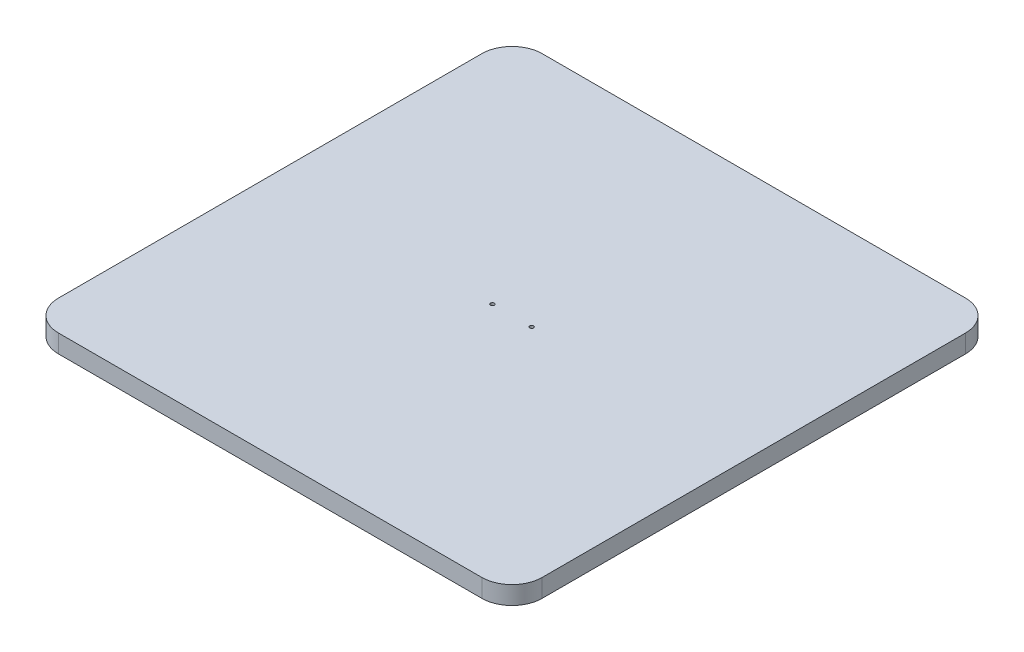
SolidWorks part; units mm, degrees
ref_plane "Front Plane" through (0, 0, 0) normal (0, 0, 1) x (1, 0, 0)
ref_plane "Top Plane" through (0, 0, 0) normal (0, 1, 0) x (1, 0, 0)
ref_plane "Right Plane" through (0, 0, 0) normal (1, 0, 0) x (0, 0, -1)
sketch "Sketch1" plane through (0, 0, 0) normal (0, 1, 0) x (1, 0, 0)
  line L1 (80, 80) -> (-80, 80)
  line L2 (80, 80) -> (80, -80)
  line L3 (80, -80) -> (-80, -80)
  line L4 (-80, 80) -> (-80, -80)
  line L5 (80, 80) -> (-80, -80) construction
  line L6 (80, -80) -> (-80, 80) construction
  point P0 (0, 0)
  dimension "D1" = 160
  dimension "D2" = 160
extrude "main body" add sketch "Sketch1" along normal blind 6
hole_wizard "M1.6 Tapped Hole1" positions "Sketch3" profile "Sketch4" tap size "M1.6" standard "ISO" end condition through all
sketch "Sketch3" plane through (0, 6, 0) normal (0, 1, 0) x (1, 0, 0)
  line L0 (-80, 0) -> (80, 0)
  line L1 (-80, 80) -> (-80, -80) construction
  line L2 (80, -80) -> (80, 80) construction
  point P7 (-6.5, 0)
  point P9 (6.5, 0)
  dimension "D1" = 6.5
  dimension "D2" = 6.5
sketch "Sketch4" plane through (6.5, 6, 0) normal (1, 0, 0) x (0, 0, 1)
  line L0 (0, 0) -> (0, 6)
  line L1 (0, 6) -> (0.625, 6)
  line L2 (0.625, 6) -> (0.625, 0)
  line L5 (0.625, 0) -> (0, 0)
  line L11 (0, -6.35) -> (0, 107.95) construction
  dimension "Thru Tap Drill Dia." = 1.25
  dimension "Thru Tap Drill Depth" = 6
cosmetic thread "Hole Thread5" parameters "D1"=10, "D2"=2.25
cosmetic thread "Hole Thread6" parameters "D1"=10, "D2"=2.25
sketch "Sketch5" plane through (0, 6, 0) normal (0, 1, 0) x (1, 0, 0)
  line L1 (20, 20) -> (-20, 20)
  line L2 (20, 20) -> (20, -20)
  line L3 (20, -20) -> (-20, -20)
  line L4 (-20, 20) -> (-20, -20)
  line L5 (20, 20) -> (-20, -20) construction
  line L6 (20, -20) -> (-20, 20) construction
  point P0 (0, 0)
  dimension "D1" = 40
  dimension "D2" = 40
extrude "Boss-Extrude2" [suppressed] add sketch "Sketch5" along normal blind 10
fillet "Fillet1" radius 10 4 edges at (-80, 3, 80) (80, 3, 80) (80, 3, -80) (-80, 3, -80)
